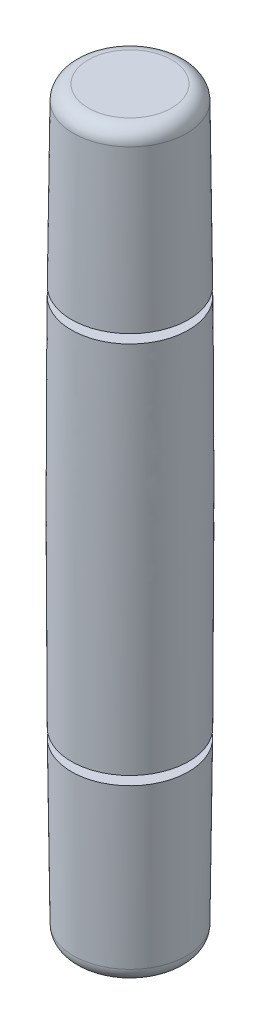
SolidWorks part; units mm, degrees
material "6061-O (SS)"
ref_plane "Plan de face" through (0, 0, 0) normal (0, 0, 1) x (1, 0, 0)
ref_plane "Plan de dessus" through (0, 0, 0) normal (0, 1, 0) x (1, 0, 0)
ref_plane "Plan de droite" through (0, 0, 0) normal (1, 0, 0) x (0, 0, -1)
sketch "Esquisse1" plane through (0, 0, 0) normal (0, 0, 1) x (1, 0, 0)
  line L0 (0, 0) -> (0, 25) construction
  line L1 (0, 25) -> (1.9, 25)
  line L2 (0, 0) -> (1.9, 0)
  line L3 (1.9, 25) -> (1.9, 0) construction
  line L4 (1.9, 12.5) -> (2, 12.5) construction
  line L5 (0, 0) -> (0, 25)
  spline S0 degree 2 poles (1.9, 25) (2.1, 12.5) (1.9, 0) knots 0 0 0 1 1 1
  dimension "D1" = 25
  dimension "D2" = 1.9
  dimension "D3" = 1.9
  dimension "D4" = 0.1
revolve "Révolution1" add sketch "Esquisse1" angle 360 about L5
fillet "Congé1" radius 0.5 2 edges at (0, 0, -1.9) (0, 25, -1.9)
sketch "Esquisse2" plane through (0, 0, 0) normal (0, 0, 1) x (1, 0, 0)
  line L0 (0, 0) -> (0, 25) construction
  line L1 (1.4078, 25) -> (-1.4078, 25) construction
  line L2 (0, 12.5) -> (0, 6.2) construction
  line L3 (0, 6.2) -> (1.9746, 6.2) construction
  line L4 (0, 12.5) -> (2, 12.5) construction
  line L5 (1.9746, 6.2) -> (1.4746, 6.2)
  line L6 (1.9746, 6.2) -> (1.9746, 5.9)
  line L7 (1.9746, 5.9) -> (1.4746, 5.9)
  line L8 (1.4746, 6.2) -> (1.4746, 5.9)
  line L9 (1.9746, 18.8) -> (1.9746, 19.1)
  line L10 (1.9746, 18.8) -> (1.4746, 18.8)
  line L11 (1.4746, 18.8) -> (1.4746, 19.1)
  line L12 (1.9746, 19.1) -> (1.4746, 19.1)
  arc A0 (1.9077, 0.4923) -> (1.9077, 24.5077) centre (-779.2961, 12.5) ccw construction
  point P14 (2.0002, 12.5)
  dimension "D1" = 6.3
  dimension "D2" = 0.3
  dimension "D3" = 0.5
revolve "Enlèvement de matière-Révolution1" cut sketch "Esquisse2" angle 360 about L0
